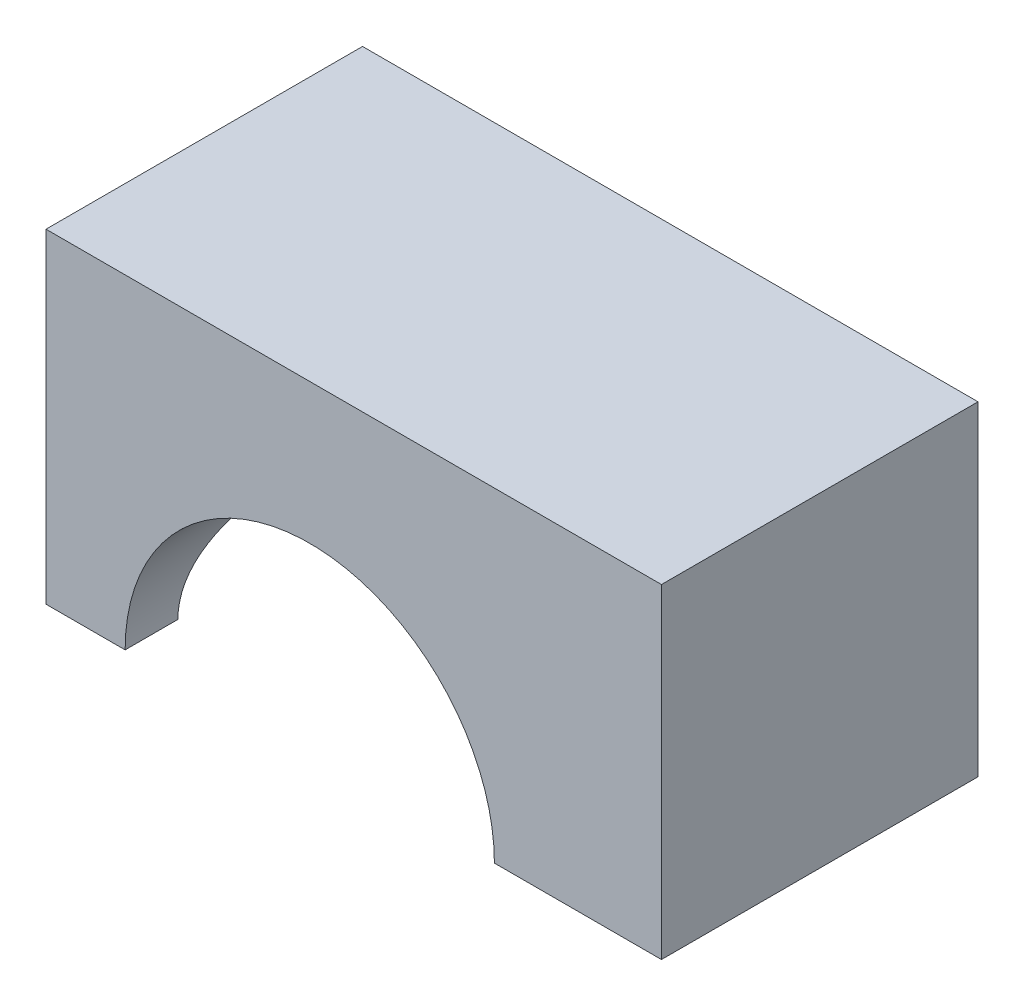
SolidWorks part; units mm, degrees
ref_plane "Front" through (0, 0, 0) normal (0, 0, 1) x (1, 0, 0)
ref_plane "Top" through (0, 0, 0) normal (0, 1, 0) x (1, 0, 0)
ref_plane "Right" through (0, 0, 0) normal (1, 0, 0) x (0, 0, -1)
sketch "Sketch1" plane through (0, 0, 0) normal (0, 1, 0) x (1, 0, 0)
  line L1 (-20, -9) -> (20, -9)
  line L2 (-20, -9) -> (-20, 9)
  line L3 (-20, 9) -> (20, 9)
  line L4 (20, -9) -> (20, 9)
  line L5 (-20, -9) -> (20, 9) construction
  line L6 (-20, 9) -> (20, -9) construction
  point P0 (0, 0)
  dimension "D1" = 40
  dimension "D2" = 18
extrude "Boss-Extrude1" add sketch "Sketch1" along normal blind 18.47
sketch "Sketch2" plane through (0, 0, 9) normal (0, 0, 1) x (1, 0, 0)
  line L0 (0, 0) -> (0, 18.47) construction
  line L1 (-20, 18.47) -> (20, 18.47) construction
  line L2 (-20, 0) -> (10, 0) construction
  line L3 (-20, 0) -> (20, 0) construction
  circle A0 centre (0, 0) radius 10.5
  dimension "D1" = 21
extrude "Cut-Extrude1" cut sketch "Sketch2" against normal up to next
sketch "Sketch4" plane through (-20, 0, 0) normal (-1, 0, 0) x (0, 0, 1)
  line L0 (-9, 0) -> (9, 0) construction
  circle A0 centre (0, 0) radius 6
  dimension "D1" = 12
extrude "Cut-Extrude3" cut sketch "Sketch4" against normal up to next
sketch "Sketch5" plane through (0, 0, 0) normal (0, -1, 0) x (1, 0, 0)
  line L0 (-10.5, -9) -> (-20, -9) construction
  line L1 (-15, 9) -> (-20, 9)
  line L2 (-15, 9) -> (-15, -9)
  line L3 (-15, -9) -> (-20, -9)
  line L4 (-20, 9) -> (-20, -9)
  line L5 (-15, 9) -> (-20, -9) construction
  line L6 (-15, -9) -> (-20, 9) construction
  line L7 (-20, -9) -> (-20, -6) construction
  point P0 (-17.5, 0)
  dimension "D1" = 0
  dimension "D2" = 0
  dimension "D3" = 5
  dimension "D4" = 0
extrude "Cut-Extrude4" cut sketch "Sketch5" against normal up to next
